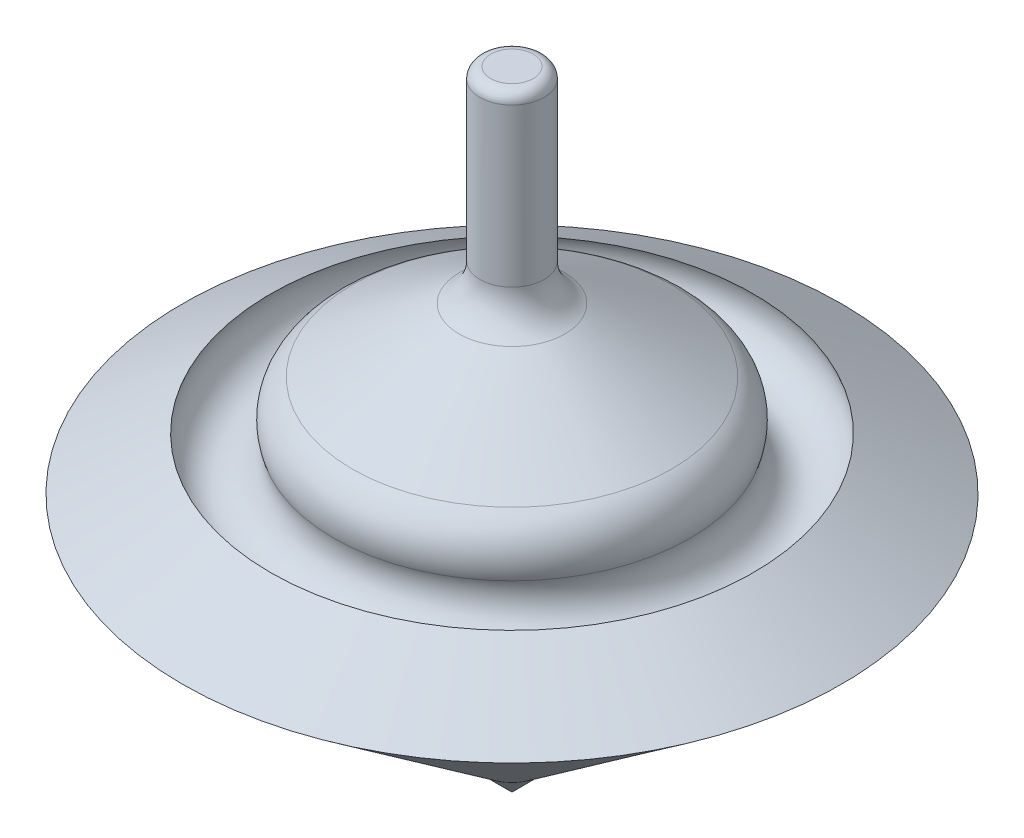
SolidWorks part; units mm, degrees
ref_plane "Front Plane" through (0, 0, 0) normal (0, 0, 1) x (1, 0, 0)
ref_plane "Top Plane" through (0, 0, 0) normal (0, 1, 0) x (1, 0, 0)
ref_plane "Right Plane" through (0, 0, 0) normal (1, 0, 0) x (0, 0, -1)
sketch "Sketch1" plane through (0, 0, 0) normal (0, 0, 1) x (1, 0, 0)
  line L0 (0, 89.7879) -> (0, -90.6042) construction
  line L1 (-6.5641, 62.4882) -> (-77.0383, 20.431)
  line L2 (-77.0383, 20.431) -> (-6.5641, -33.3719)
  line L3 (-6.5641, -33.3719) -> (-6.5641, 62.4882)
sketch "Sketch3" plane through (0, 0, 0) normal (0, 0, 1) x (1, 0, 0)
revolve "Revolve1" add sketch "Sketch1" angle 360 about L0
sketch "Sketch4" plane through (0, 0, 0) normal (0, 1, 0) x (1, 0, 0)
  circle A0 centre (0, 0) radius 7.5
  dimension "D1" = 15
extrude "Boss-Extrude1" add sketch "Sketch4" along normal blind 107 contours A0
sketch "Sketch7" plane through (0, 0, 0) normal (1, 0, 0) x (0, 0, -1)
  line L0 (0, -49.3036) -> (0, -24.5015) construction
  line L1 (-6.5641, -33.3719) -> (-0.2899, -39.6461)
  line L2 (-6.5641, -33.3719) -> (6.5641, -33.3719) construction
  line L3 (-0.2899, -39.6461) -> (-0.2899, -33.3719)
  line L4 (-0.2899, -33.3719) -> (-6.5641, -33.3719)
revolve "Revolve2" add sketch "Sketch7" angle 360 about L0
sketch "Sketch8" plane through (0, 0, 0) normal (0, 0, 1) x (1, 0, 0)
  line L0 (0, -84.7422) -> (0, 84.7422) construction
  line L1 (0, 59.502) -> (0, 5.962) construction
  line L2 (-42.9639, 35.3738) -> (-43.6684, 35.3738) construction
  circle A0 centre (-49.1281, 29.738) radius 7.894
  circle A1 centre (49.1281, 29.738) radius 7.894
revolve "Cut-Revolve1" cut sketch "Sketch8" angle 360 about L1
fillet "Fillet1" radius 10 2 edges at (0, 61.9297, -7.5) (0, 37.5873, -48.2899)
fillet "Fillet4" radius 2.54 1 edges at (0, 107, 7.5)
